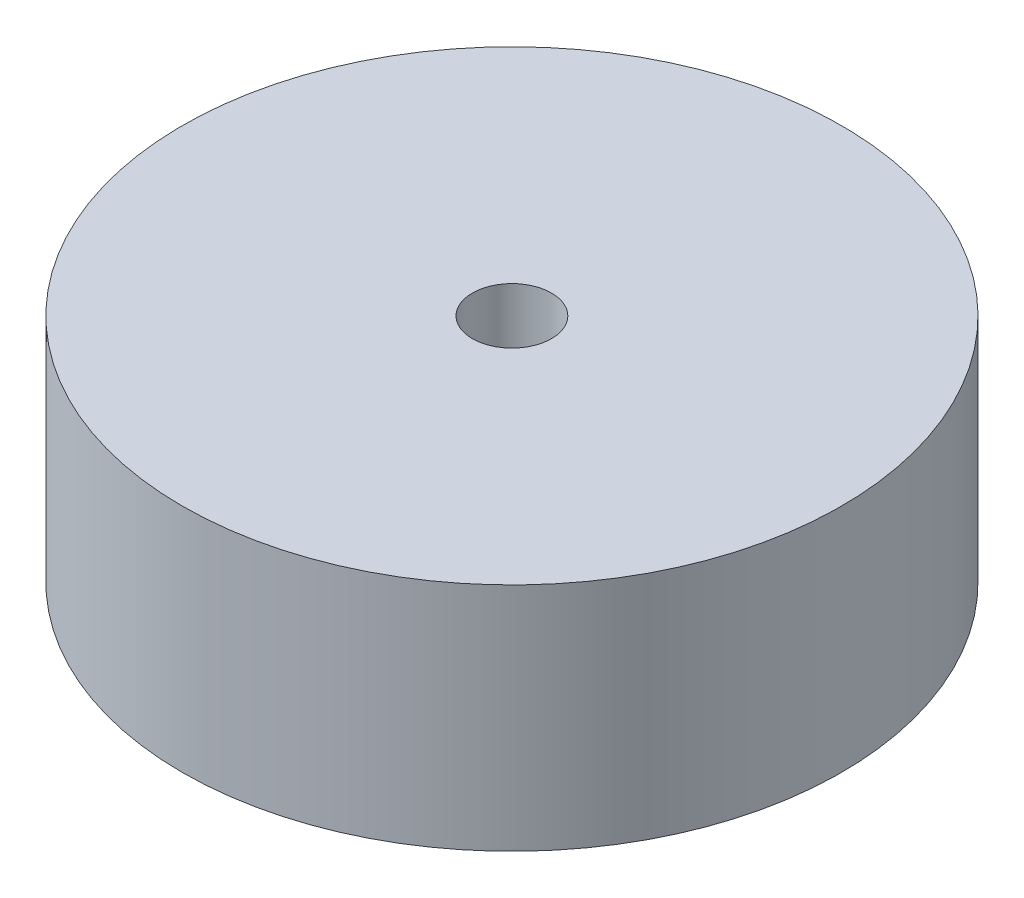
SolidWorks part; units mm, degrees
ref_plane "Front Plane" through (0, 0, 0) normal (0, 0, 1) x (1, 0, 0)
ref_plane "Top Plane" through (0, 0, 0) normal (0, 1, 0) x (1, 0, 0)
ref_plane "Right Plane" through (0, 0, 0) normal (1, 0, 0) x (0, 0, -1)
sketch "Sketch1" plane through (0, 0, 0) normal (0, 1, 0) x (1, 0, 0)
  circle A0 centre (0, 0) radius 50
  circle A1 centre (0, 0) radius 6
  point P4 (0, 0)
  dimension "D1" = 12
  dimension "D2" = 100
extrude "Boss-Extrude1" add sketch "Sketch1" along normal blind 35
